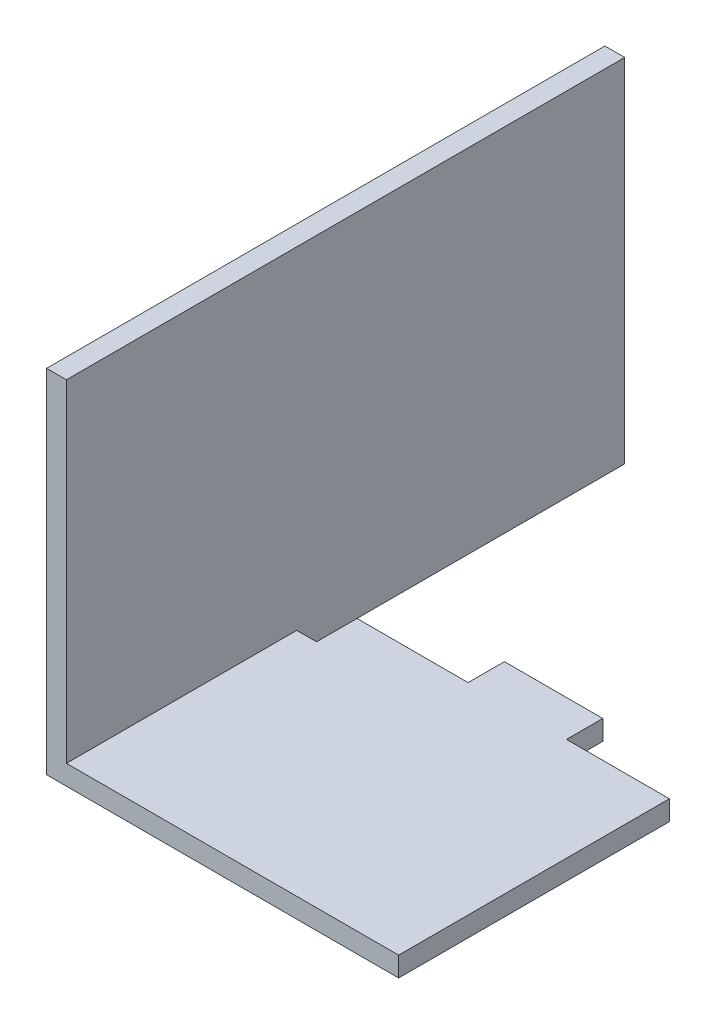
SolidWorks part; units mm, degrees
ref_plane "Front" through (0, 0, 0) normal (0, 0, 1) x (1, 0, 0)
ref_plane "Top" through (0, 0, 0) normal (0, 1, 0) x (1, 0, 0)
ref_plane "Right" through (0, 0, 0) normal (1, 0, 0) x (0, 0, -1)
sketch "Sketch1" plane through (0, 0, 0) normal (0, 0, 1) x (1, 0, 0)
  line L0 (0, 0) -> (0, -25.22)
  line L1 (25.22, -25.22) -> (0, -25.22)
  line L2 (25.22, -25.22) -> (25.22, -23.8)
  line L3 (25.22, -23.8) -> (1.42, -23.8)
  line L4 (1.42, 0) -> (1.42, -23.8)
  line L5 (1.42, 0) -> (0, 0)
extrude "Extrude1" add sketch "Sketch1" along normal blind 40
sketch "Sketch3" plane through (0, -23.8, 0) normal (0, 1, 0) x (-1, 0, 0)
  line L9 (-25.22, 40) -> (-25.22, 0) construction
  line L13 (-25.22, 0) -> (-25.22, 20.6)
  line L14 (-25.22, 20.6) -> (-17.85, 20.6)
  line L15 (-17.85, 20.6) -> (-17.85, 18)
  line L16 (-17.85, 18) -> (-10.8, 18)
  line L17 (-10.8, 18) -> (-10.8, 20.6)
  line L18 (-10.8, 20.6) -> (-2.84, 20.6)
  line L19 (-2.84, 20.6) -> (-2.84, 23.5)
  line L20 (-2.84, 23.5) -> (-1.42, 23.5)
  line L21 (-1.42, 23.5) -> (-1.42, 0)
  line L22 (-1.42, 0) -> (-25.22, 0)
extrude "Cut-Extrude3" cut sketch "Sketch3" against normal through all
